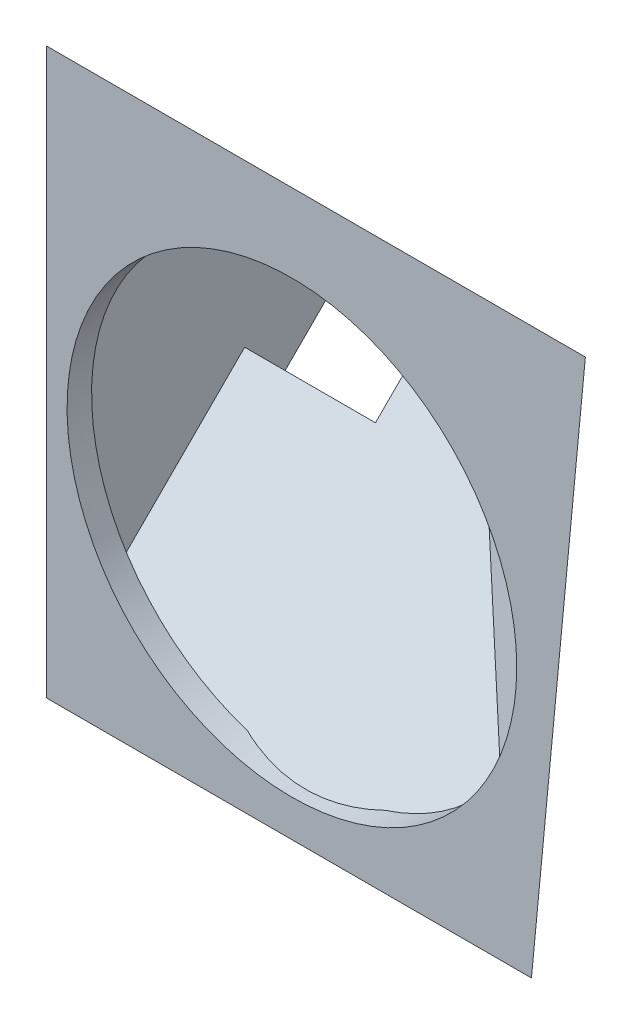
SolidWorks part; units mm, degrees
ref_plane "Front Plane" through (0, 0, 0) normal (0, 0, 1) x (1, 0, 0)
ref_plane "Top Plane" through (0, 0, 0) normal (0, 1, 0) x (1, 0, 0)
ref_plane "Right Plane" through (0, 0, 0) normal (1, 0, 0) x (0, 0, -1)
sketch "Sketch1" plane through (0, 0, 0) normal (0, 0, 1) x (1, 0, 0)
  line L0 (-2, 58) -> (58, -2) construction
  line L5 (-2, 58) -> (58, 58)
  line L6 (-2, 58) -> (-2, -2)
  line L7 (-2, -2) -> (58, -2)
  line L8 (58, 58) -> (58, -2)
  circle A0 centre (28, 28) radius 27.5
  dimension "D1" = 55
  dimension "D3" = 60
  dimension "D4" = 60
extrude "Boss-Extrude2" add sketch "Sketch1" along normal blind 2
sketch "Sketch2" plane through (-2, 0, 0) normal (-1, 0, 0) x (0, 0, 1)
  line L0 (2, 58) -> (-1.5355, 61.5355)
  line L1 (-1.5355, 61.5355) -> (-32.5355, 30.5355)
  line L2 (-32.5355, 30.5355) -> (0, -2)
  line L7 (0, 58) -> (0, -2)
  line L8 (0, -2) -> (2, -2)
  line L9 (2, -2) -> (2, 58)
  line L10 (2, 58) -> (0, 58)
  line L11 (0, 58) -> (0, -2)
  line L14 (2, 58) -> (0, 58)
  dimension "D1" = 90
  dimension "D3" = 5
  dimension "D2" = 0
extrude "Boss-Extrude3" add sketch "Sketch2" against normal blind 1
sketch "Sketch3" plane through (-1, 0, 0) normal (1, 0, 0) x (0, 0, -1)
  line L0 (0, 58) -> (2.5355, 60.5355)
  line L1 (1.5355, 61.5355) -> (32.5355, 30.5355) construction
  line L2 (2.5355, 60.5355) -> (1.5355, 61.5355)
  line L3 (1.5355, 61.5355) -> (-2, 58)
  line L4 (-2, 58) -> (0, 58)
extrude "Boss-Extrude4" add sketch "Sketch3" along normal up to surface (59 mm away) up to face at (58, 28, 1)
sketch "Sketch5" plane through (-1, 0, 0) normal (1, 0, 0) x (0, 0, -1)
  line L0 (2.5355, 60.5355) -> (32.5355, 30.5355)
  line L1 (32.5355, 30.5355) -> (31.1213, 29.1213)
  line L2 (32.5355, 30.5355) -> (0, -2) construction
  line L3 (31.1213, 29.1213) -> (1.1213, 59.1213)
  line L4 (0, 58) -> (2.5355, 60.5355) construction
  line L5 (1.1213, 59.1213) -> (2.5355, 60.5355)
  dimension "D1" = 2
extrude "Boss-Extrude5" add sketch "Sketch5" along normal blind 20
sketch "Sketch6" plane through (0, 31.5355, -31.5355) normal (0, 0.7071, -0.7071) x (1, 0, 0)
  line L0 (-2, -42.4264) -> (-2, 1.4142) construction
  line L1 (0.5, -1.2687) -> (4.5, -1.2687)
  line L2 (0.5, -1.2687) -> (0.5, -16.1169)
  line L3 (0.5, -16.1169) -> (4.5, -16.1169)
  line L4 (4.5, -1.2687) -> (4.5, -16.1169)
  dimension "D1" = 4
  dimension "D2" = 2.5
extrude "Cut-Extrude1" cut sketch "Sketch6" against normal blind 20
sketch "Sketch7" plane through (0, 31.5355, -31.5355) normal (0, 0.7071, -0.7071) x (1, 0, 0)
  line L0 (19, 1.4142) -> (58, -41.0122)
  line L1 (58, -41.0122) -> (19, -41.0122)
  line L2 (19, -41.0122) -> (19, 1.4142)
extrude "Boss-Extrude6" add sketch "Sketch7" against normal up to surface (2 mm away) up to face at (2.5, 36.2681, -23.9746)
sketch "Sketch9" plane through (0, -1, -1) normal (0, -0.7071, -0.7071) x (-1, 0, 0)
  line L0 (2, 44.598) -> (2, -1.4142) construction
  line L1 (2, 30.598) -> (-19, 30.598)
  line L2 (2, 30.598) -> (2, -2.8284)
  line L3 (2, -2.8284) -> (-19, -2.8284)
  line L4 (-19, 30.598) -> (-19, -2.8284)
  line L5 (-19, 42.598) -> (1, 42.598) construction
  line L6 (2, -2.8284) -> (-58, -2.8284) construction
  dimension "D1" = 12
  dimension "D2" = 0
extrude "Boss-Extrude8" add sketch "Sketch9" against normal blind 2
ref_plane "Plane2" through (22.4693, -2.1452, -27.0649) normal (0.6376, -0.0609, -0.768) x (-0.6768, -0.5206, -0.5206)
sketch "Sketch11" plane through (22.4693, -2.1452, -27.0649) normal (0.6376, -0.0609, -0.768) x (-0.6768, -0.5206, -0.5206)
  line L1 (-69.3964, 31.0653) -> (-11.6773, 31.0653)
  line L2 (-69.3964, 31.0653) -> (-69.3964, -28.8411)
  line L3 (-69.3964, -28.8411) -> (-11.6773, -28.8411)
  line L4 (-11.6773, 31.0653) -> (-11.6773, -28.8411)
extrude "Boss-Extrude9" add sketch "Sketch11" against normal blind 1.5
sketch "Sketch12" plane through (21.513, -2.0539, -25.913) normal (-0.6376, 0.0609, 0.768) x (0.7704, 0.0504, 0.6356)
  line L0 (43.6496, -2.1518) -> (42.7246, -9.5924)
  line L1 (74.7427, 7.8231) -> (24.0389, -19.7561) construction
  line L2 (42.7246, -9.5924) -> (74.7427, 7.8231)
  line L3 (74.7427, 7.8231) -> (47.3177, 58.2433)
  line L4 (47.2682, 58.3344) -> (74.7427, 7.8231) construction
  line L5 (47.3177, 58.2433) -> (43.6496, -2.1518)
extrude "Cut-Extrude3" cut sketch "Sketch12" against normal through all
sketch "Sketch13" plane through (19, 0, 0) normal (1, 0, 0) x (0, 0, -1)
  line L0 (21.2218, 22.0503) -> (22.636, 20.636)
  line L1 (22.636, 20.636) -> (-1, -3)
  line L2 (-1, -3) -> (-2.4142, -1.5858)
  line L3 (-2.4142, -1.5858) -> (21.2218, 22.0503)
extrude "Boss-Extrude10" add sketch "Sketch13" along normal up to surface (36.6785 mm away)
sketch "Sketch14" plane through (21.513, -2.0539, -25.913) normal (-0.6376, 0.0609, 0.768) x (0.7704, 0.0504, 0.6356)
  line L0 (41.9621, -3.0696) -> (7.9355, 22.3601)
  line L1 (7.9355, 22.3601) -> (-27.7756, 49.0488)
  line L2 (-27.7756, 49.0488) -> (11.8689, -40.1065)
  line L3 (11.8689, -40.1065) -> (63.9125, -11.7325)
  line L4 (63.9125, -11.7325) -> (41.9621, -3.0696)
extrude "Cut-Extrude4" cut sketch "Sketch14" against normal blind 26.5
sketch "Sketch15" plane through (0, -1, -1) normal (0, -0.7071, -0.7071) x (-1, 0, 0)
  line L1 (8.0183, -11.1421) -> (-90.7774, -11.1421)
  line L2 (8.0183, -11.1421) -> (8.0183, 58.1098)
  line L3 (8.0183, 58.1098) -> (-90.7774, 58.1098)
  line L4 (-90.7774, -11.1421) -> (-90.7774, 58.1098)
extrude "Cut-Extrude5" cut sketch "Sketch15" along normal blind 59.5
sketch "Sketch16" plane through (22.4693, -2.1452, -27.0649) normal (0.6376, -0.0609, -0.768) x (-0.7704, -0.0504, -0.6356)
  circle A0 centre (-31.476, 28.9091) radius 67.6686
extrude "Cut-Extrude6" cut sketch "Sketch16" along normal blind 1093.5
sketch "Sketch17" plane through (58, 0, 0) normal (1, 0, 0) x (0, 0, -1)
  circle A0 centre (-1.2301, 56.9339) radius 80.4148
extrude "Cut-Extrude7" cut sketch "Sketch17" along normal blind 212.5
sketch "Sketch18" plane through (0, 0, 2) normal (0, 0, 1) x (1, 0, 0)
  line L1 (68.6219, -9.9445) -> (-12.6219, -9.9445)
  line L2 (68.6219, -9.9445) -> (68.6219, 65.9445)
  line L3 (68.6219, 65.9445) -> (-12.6219, 65.9445)
  line L4 (-12.6219, -9.9445) -> (-12.6219, 65.9445)
  line L5 (68.6219, -9.9445) -> (-12.6219, 65.9445) construction
  line L6 (68.6219, 65.9445) -> (-12.6219, -9.9445) construction
  circle A0 centre (28, 28) radius 27.5
  point P0 (28, 28)
extrude "Boss-Extrude12" add sketch "Sketch18" against normal blind 3
sketch "Sketch19" plane through (22.4693, -2.1452, -27.0649) normal (0.6376, -0.0609, -0.768) x (-0.7704, -0.0504, -0.6356)
  line L0 (-40.8954, -0.9179) -> (4.3526, 32.8981)
  line L1 (-40.8954, -0.9179) -> (4.4283, 32.9547) construction
  line L2 (4.3526, 32.8981) -> (-69.9676, 73.353)
  line L3 (-40.8954, -0.9179) -> (-46.1205, 41.113)
  line L4 (-46.1205, 41.113) -> (-48.6886, 61.7702)
  line M1 (-46.1205, 60.4443) -> (-46.1205, 41.113)
  line M2 (-46.1205, 41.113) -> (-40.8954, -0.9179)
  line M3 (-40.8954, -0.9179) -> (4.4283, 32.9547)
extrude "Boss-Extrude13" add sketch "Sketch19" against normal blind 2 contours L4 L2 M1 | L2 M3 M1 M2
sketch "Sketch20" plane through (22.4693, -2.1452, -27.0649) normal (0.6376, -0.0609, -0.768) x (-0.7704, -0.0504, -0.6356)
  circle A0 centre (-26.945, 29.3881) radius 82.6362
extrude "Cut-Extrude8" cut sketch "Sketch20" along normal blind 100
sketch "Sketch21" plane through (0, 31.5355, -31.5355) normal (0, 0.7071, -0.7071) x (1, 0, 0)
  circle A0 centre (19.5905, -26.7237) radius 85.0463
extrude "Cut-Extrude9" cut sketch "Sketch21" along normal blind 22
sketch "Sketch23" plane through (-2, 0, 0) normal (-1, 0, 0) x (0, 0, 1)
  circle A0 centre (-13.3616, 29.2879) radius 93.1599
extrude "Cut-Extrude11" cut sketch "Sketch23" along normal blind 94
sketch "Sketch24" plane through (0, -1, -1) normal (0, -0.7071, -0.7071) x (-1, 0, 0)
  circle A0 centre (-12.7398, 17.8686) radius 86.2814
extrude "Cut-Extrude12" cut sketch "Sketch24" along normal blind 48
sketch "Sketch25" plane through (0, 0, 2) normal (0, 0, 1) x (1, 0, 0)
  circle A0 centre (30.3558, 29.2129) radius 66.1984
extrude "Cut-Extrude13" cut sketch "Sketch25" along normal blind 170
sketch "Sketch26" plane through (0, -1, -1) normal (0, -0.7071, -0.7071) x (-1, 0, 0)
  line L0 (-15, 30.598) -> (-15, 44.598)
  line L1 (1, 30.598) -> (-27.6264, 30.598) construction
  line L2 (-19, 44.598) -> (2, 44.598) construction
  line L3 (-15, 44.598) -> (-18.3254, 44.598)
  line L4 (-18.3254, 44.598) -> (-30.1508, 29.4631)
  line L5 (-30.1508, 29.4631) -> (-15, 29.4631)
  line L6 (-15, 29.4631) -> (-15, 30.598)
  line L7 (1, 42.598) -> (1, 30.598) construction
  dimension "D1" = 16
extrude "Boss-Extrude14" add sketch "Sketch26" against normal up to surface (2 mm away) up to face at (22.2981, 8.3476, -7.5192)
sketch "Sketch27" plane through (0, -1, -1) normal (0, -0.7071, -0.7071) x (-1, 0, 0)
  line L1 (1, 42.598) -> (-15, 42.598)
  line L2 (1, 42.598) -> (1, 30.598)
  line L3 (1, 30.598) -> (-15, 30.598)
  line L4 (-15, 42.598) -> (-15, 30.598)
  line L5 (2, 44.598) -> (-16.5, 44.598)
  line L6 (2, 44.598) -> (2, 29.098)
  line L7 (2, 29.098) -> (-16.5, 29.098)
  line L8 (-16.5, 44.598) -> (-16.5, 29.098)
  dimension "D1" = 1.5
  dimension "D2" = 1.5
extrude "Boss-Extrude15" add sketch "Sketch27" along normal blind 5
